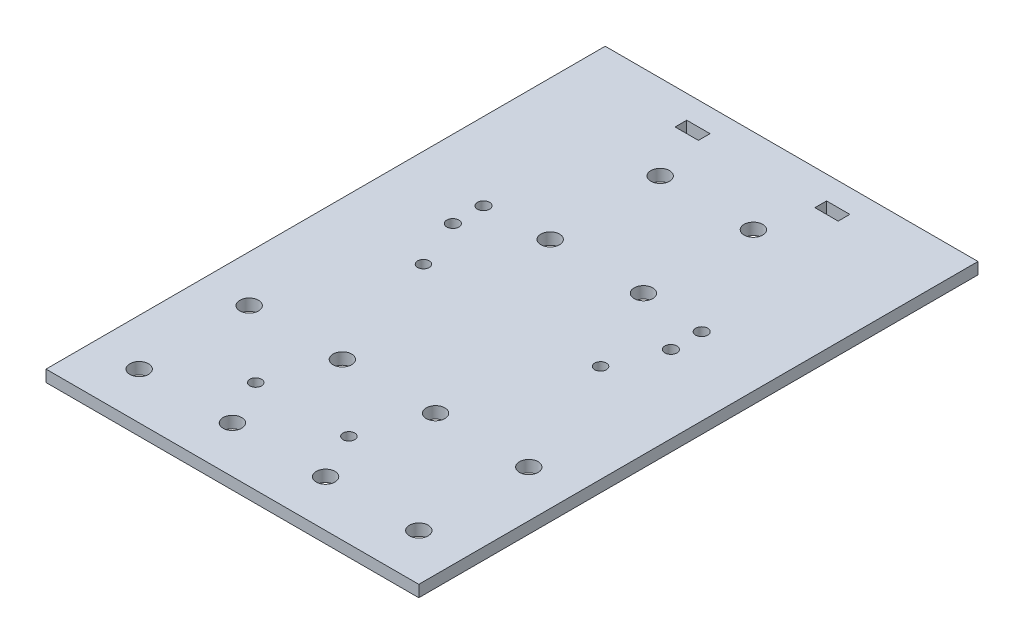
SolidWorks part; units mm, degrees
ref_plane "Front Plane" through (0, 0, 0) normal (0, 0, 1) x (1, 0, 0)
ref_plane "Top Plane" through (0, 0, 0) normal (0, 1, 0) x (1, 0, 0)
ref_plane "Right Plane" through (0, 0, 0) normal (1, 0, 0) x (0, 0, -1)
sketch "Sketch2" plane through (0, 0, 0) normal (0, 1, 0) x (1, 0, 0)
  line L1 (-50.8, -76.2) -> (50.8, -76.2)
  line L2 (-50.8, -76.2) -> (-50.8, 76.2)
  line L3 (-50.8, 76.2) -> (50.8, 76.2)
  line L4 (50.8, -76.2) -> (50.8, 76.2)
  line L5 (-50.8, -76.2) -> (50.8, 76.2) construction
  line L6 (-50.8, 76.2) -> (50.8, -76.2) construction
  point P0 (0, 0)
  dimension "D1" = 101.6
  dimension "D2" = 152.4
extrude "Boss-Extrude1" add sketch "Sketch2" along normal blind 3.175
sketch "Sketch3" plane through (0, 3.175, 0) normal (0, 1, 0) x (1, 0, 0)
  line L0 (0, 76.2) -> (0, -76.2) construction
  line L1 (50.8, 76.2) -> (-50.8, 76.2) construction
  line L2 (-50.8, -76.2) -> (50.8, -76.2) construction
  line L3 (-50.8, 0) -> (50.8, 0) construction
  line L4 (-50.8, 76.2) -> (-50.8, -76.2) construction
  line L5 (50.8, -76.2) -> (50.8, 76.2) construction
  circle A0 centre (-38.1, -63.5) radius 2.54
  circle A12 centre (-12.7, -63.5) radius 2.54
  circle A13 centre (12.7, -63.5) radius 2.54
  circle A14 centre (38.1, -63.5) radius 2.54
  circle A15 centre (-38.1, -33.528) radius 2.54
  circle A16 centre (-12.7, -33.528) radius 2.54
  circle A17 centre (12.7, -33.528) radius 2.54
  circle A18 centre (38.1, -33.528) radius 2.54
  circle A19 centre (-12.7, 53.086) radius 2.54
  circle A20 centre (-12.7, 23.114) radius 2.54
  circle A21 centre (12.7, 23.114) radius 2.54
  circle A22 centre (12.7, 53.086) radius 2.54
  dimension "D5" = 2
  dimension "D6" = 5.08
  dimension "D1" = 12.7
  dimension "D2" = 12.7
  dimension "D3" = 4
  dimension "D4" = 2
extrude "Cut-Extrude1" cut sketch "Sketch3" against normal through all
sketch "Sketch4" plane through (0, 3.175, 0) normal (0, 1, 0) x (1, 0, 0)
  line L0 (-12.7, 53.086) -> (12.7, 23.114) construction
  line L1 (12.7, 53.086) -> (-12.7, 23.114) construction
  line L2 (-50.8, 38.1) -> (50.8, 38.1) construction
  line L3 (50.8, -76.2) -> (50.8, 76.2) construction
  line L4 (-50.8, 17.78) -> (50.8, 17.78) construction
  line L5 (-50.8, 76.2) -> (-50.8, -76.2) construction
  line L6 (0, 76.2) -> (0, -76.2) construction
  line L7 (50.8, 76.2) -> (-50.8, 76.2) construction
  line L8 (-50.8, -76.2) -> (50.8, -76.2) construction
  circle A2 centre (29.718, 13.589) radius 1.651
  circle A3 centre (29.718, 21.971) radius 1.651
  circle A4 centre (-29.718, 21.971) radius 1.651
  circle A5 centre (-29.718, 13.589) radius 1.651
  point P14 (0, 38.1)
  dimension "D3" = 3.302
  dimension "D1" = 20.32
  dimension "D2" = 4.191
  dimension "D4" = 21.082
extrude "Cut-Extrude2" cut sketch "Sketch4" against normal through all
sketch "Sketch5" plane through (0, 3.175, 0) normal (0, 1, 0) x (1, 0, 0)
  line L0 (0, 76.2) -> (0, -76.2) construction
  line L1 (50.8, 76.2) -> (-50.8, 76.2) construction
  line L2 (-50.8, -76.2) -> (50.8, -76.2) construction
  line L3 (-50.8, 0) -> (50.8, 0) construction
  line L4 (-50.8, 76.2) -> (-50.8, -76.2) construction
  line L5 (50.8, -76.2) -> (50.8, 76.2) construction
  line L6 (-19.05, 76.2) -> (-19.05, -76.2) construction
  circle A0 centre (-24.13, 0) radius 1.5875
  circle A1 centre (24.13, 0) radius 1.5875
  circle A2 centre (-19.05, -50.8) radius 1.5875
  circle A3 centre (6.35, -50.8) radius 1.5875
  dimension "D1" = 3.175
  dimension "D2" = 24.13
  dimension "D3" = 5.08
  dimension "D4" = 3.175
  dimension "D5" = 50.8
  dimension "D6" = 2
extrude "Cut-Extrude3" cut sketch "Sketch5" against normal through all
sketch "Sketch6" plane through (0, 3.175, 0) normal (0, 1, 0) x (1, 0, 0)
  line L0 (0, 76.2) -> (0, -76.2) construction
  line L1 (50.8, 76.2) -> (-50.8, 76.2) construction
  line L2 (-50.8, -76.2) -> (50.8, -76.2) construction
  line L3 (-50.8, 0) -> (50.8, 0) construction
  line L4 (-50.8, 76.2) -> (-50.8, -76.2) construction
  line L5 (50.8, -76.2) -> (50.8, 76.2) construction
  line L6 (22.225, 66.675) -> (15.875, 66.675)
  line L7 (-22.225, 69.85) -> (-15.875, 69.85)
  line L8 (-22.225, 69.85) -> (-22.225, 66.675)
  line L9 (-22.225, 66.675) -> (-15.875, 66.675)
  line L10 (-15.875, 69.85) -> (-15.875, 66.675)
  line L11 (15.875, 69.85) -> (15.875, 66.675)
  line L12 (22.225, 69.85) -> (15.875, 69.85)
  line L13 (22.225, 69.85) -> (22.225, 66.675)
  point P16 (-15.875, 68.2625)
  dimension "D1" = 22.225
  dimension "D2" = 3.175
  dimension "D3" = 6.35
  dimension "D4" = 6.35
extrude "Cut-Extrude4" cut sketch "Sketch6" against normal through all
